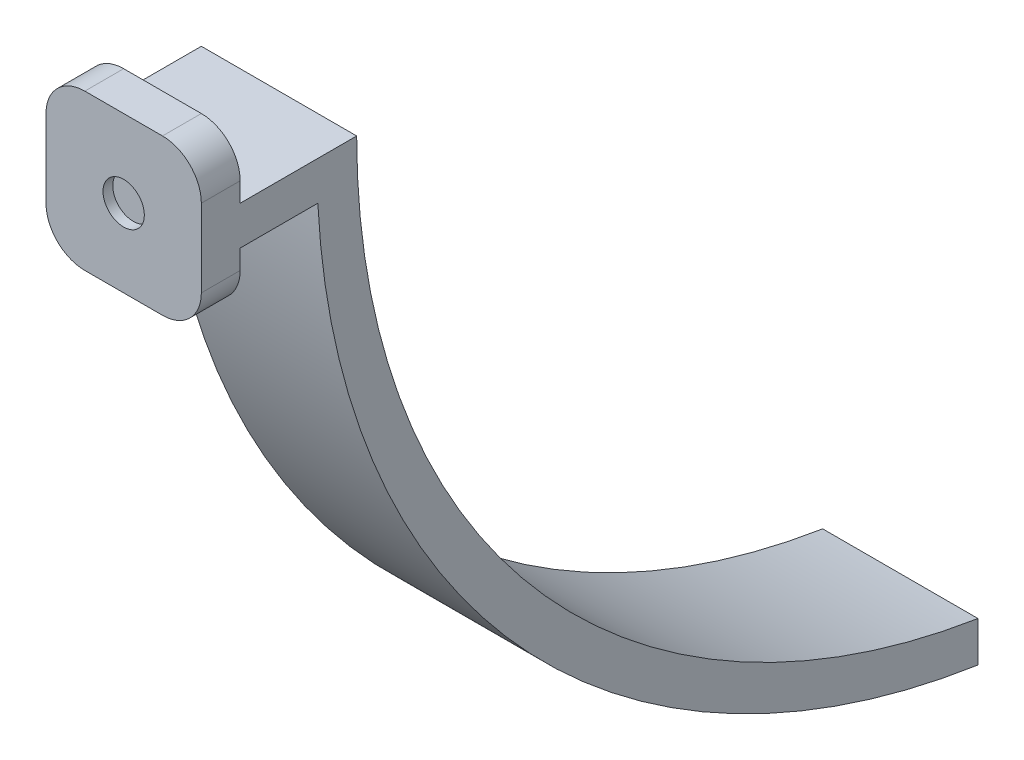
SolidWorks part; units mm, degrees
material "PET"
ref_plane "Front Plane" through (0, 0, 0) normal (0, 0, 1) x (1, 0, 0)
ref_plane "Top Plane" through (0, 0, 0) normal (0, 1, 0) x (1, 0, 0)
ref_plane "Right Plane" through (0, 0, 0) normal (1, 0, 0) x (0, 0, -1)
sketch "Sketch1" plane through (0, 0, 0) normal (1, 0, 0) x (0, 0, -1)
  line L0 (0, 0) -> (0, 25.4)
  line L1 (0, 25.4) -> (6.35, 25.4)
  line L2 (6.35, 25.4) -> (6.35, 15.875)
  line L6 (6.35, 9.525) -> (6.35, 0)
  line L7 (6.35, 0) -> (0, 0)
  line L8 (6.35, 15.875) -> (25.4, 15.875)
  line L9 (6.35, 9.525) -> (19.05, 9.525)
  line L10 (127, -103.2616) -> (127, -109.8486)
  arc A2 (19.05, 9.525) -> (127, -109.8486) centre (146.05, 15.875) ccw
  arc A3 (25.4, 15.875) -> (127, -103.2616) centre (146.05, 15.875) ccw
  dimension "D2" = 6.35
  dimension "D3" = 120.65
  dimension "D1" = 6.35
  dimension "D4" = 101.6
  dimension "D5" = 6.35
  dimension "D6" = 25.4
  dimension "D7" = 12.7
extrude "Boss-Extrude1" add sketch "Sketch1" along normal mid plane 25.4
sketch "Sketch2" plane through (0, 0, 0) normal (0, 0, 1) x (1, 0, 0)
  line L0 (12.7, 0) -> (-12.7, 0) construction
  circle A0 centre (0, 12.7) radius 3.3782
  point P4 (0, 0)
  point P5 (0, 0)
  dimension "D2" = 6.7564
  dimension "D1" = 12.7
extrude "Cut-Extrude1" cut sketch "Sketch2" against normal blind 1.5875
fillet "Fillet2" radius 6.35 4 edges at (-12.7, 0, -3.175) (12.7, 0, -3.175) (12.7, 25.4, -3.175) (-12.7, 25.4, -3.175)
